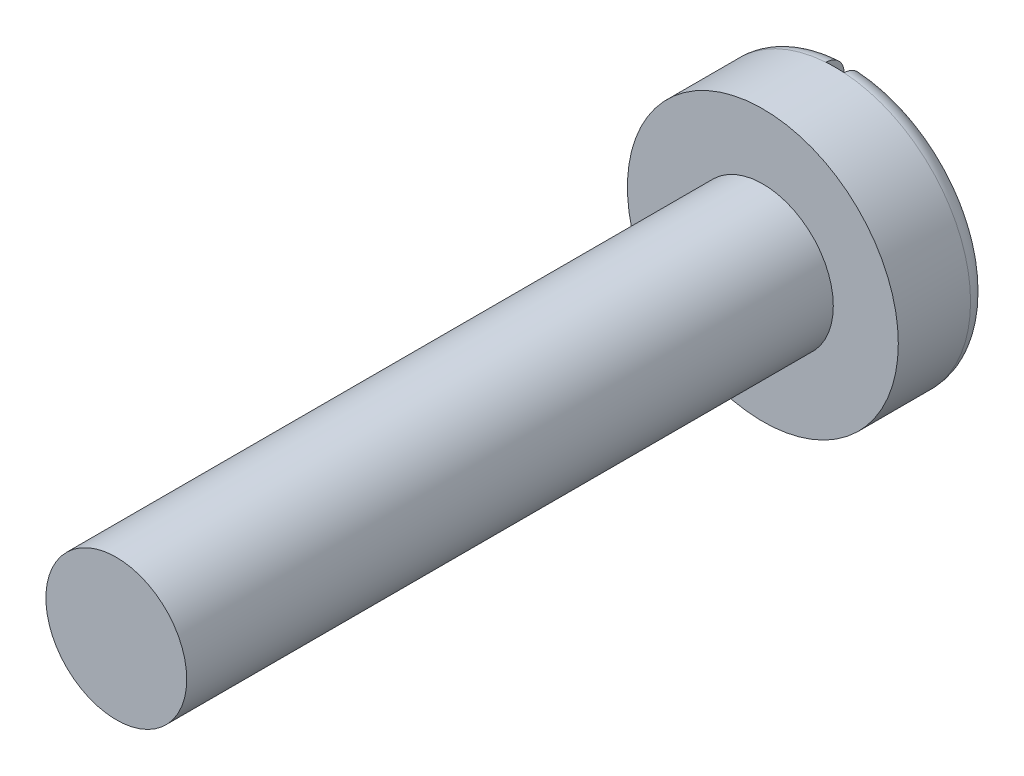
SolidWorks part; units mm, degrees
ref_plane "Front Plane" through (0, 0, 0) normal (0, 0, 1) x (1, 0, 0)
ref_plane "Top Plane" through (0, 0, 0) normal (0, 1, 0) x (1, 0, 0)
ref_plane "Right Plane" through (0, 0, 0) normal (1, 0, 0) x (0, 0, -1)
ref_axis "Axis1" through (0, 0, 55) along (0, 0, -1)
sketch "Sketch3" plane through (0, 0, 0) normal (1, 0, 0) x (0, 0, -1)
  line L1 (0, 1.905) -> (1.27, 1.905)
  line L2 (1.27, 1.905) -> (1.27, 0)
  line L3 (-55, 0) -> (55, 0) construction
  line L4 (1.27, 0) -> (0, 0)
  line L6 (0, 0.9906) -> (-9.0932, 0.9906)
  line L7 (-9.0932, 0.9906) -> (-9.0932, 0)
  line L8 (-9.0932, 0) -> (0, 0)
  line L9 (0, 1.905) -> (0, 0.9906)
revolve "Revolve1" add sketch "Sketch3" angle 360 about axis through (0, 0, 55) along (0, 0, -1)
sketch "Sketch4" plane through (0, 0, -1.27) normal (0, 0, -1) x (-1, 0, 0)
  line L0 (0, 1.905) -> (0, -1.905)
  line L1 (-0.127, 1.905) -> (-0.127, -1.905)
  line L2 (0.127, 1.905) -> (0.127, -1.905)
  line L3 (-0.127, 1.905) -> (0.127, 1.905)
  line L4 (0.127, -1.905) -> (-0.127, -1.905)
  circle A1 centre (0, 0) radius 1.905 construction
  circle M6 centre (0, 0) radius 1.905
  dimension "D1" = 0.127
  dimension "D2" = 0.127
extrude "Cut-Extrude1" cut sketch "Sketch4" against normal blind 0.254 contours L1 L0 M6 | L2 L0 M6
fillet "Fillet1" radius 0.254 2 edges at (-1.905, 0, -1.27) (1.905, 0, -1.27)
